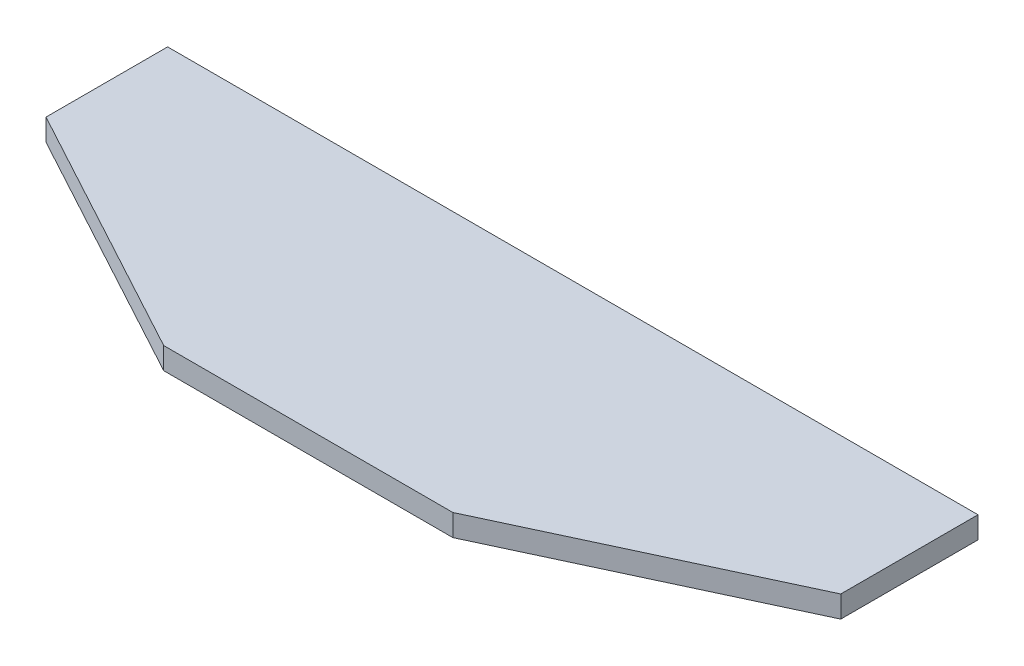
SolidWorks part; units mm, degrees
ref_plane "Alzado" through (0, 0, 0) normal (0, 0, 1) x (1, 0, 0)
ref_plane "Planta" through (0, 0, 0) normal (0, 1, 0) x (1, 0, 0)
ref_plane "Vista lateral" through (0, 0, 0) normal (1, 0, 0) x (0, 0, -1)
sketch "Croquis1" plane through (0, 0, 0) normal (0, 1, 0) x (1, 0, 0)
  line L0 (-34.0814, -32.3154) -> (32.2774, -32.3154)
  line L2 (93, -4) -> (93, 27.5)
  line L3 (93, 27.5) -> (-93, 27.5)
  line L4 (-93, -0.4156) -> (-93, 27.5)
  line L5 (62.1604, -18.3808) -> (-93, 27.5) construction
  line L6 (93, 27.5) -> (-60.6458, -17.9329) construction
  line L7 (32.2774, -32.3154) -> (93, -4)
  line L8 (-34.0814, -32.3154) -> (-93, -0.4156)
  point P0 (0, 0)
  point P9 (-0.902, -32.3154)
  dimension "D1" = 186
  dimension "D2" = 67
  dimension "D3" = 155
  dimension "D4" = 151.568
  dimension "D5" = 67
  dimension "D6" = 66.3588
  dimension "D7" = 31.5
extrude "Saliente-Extruir1" add sketch "Croquis1" along normal blind 5
